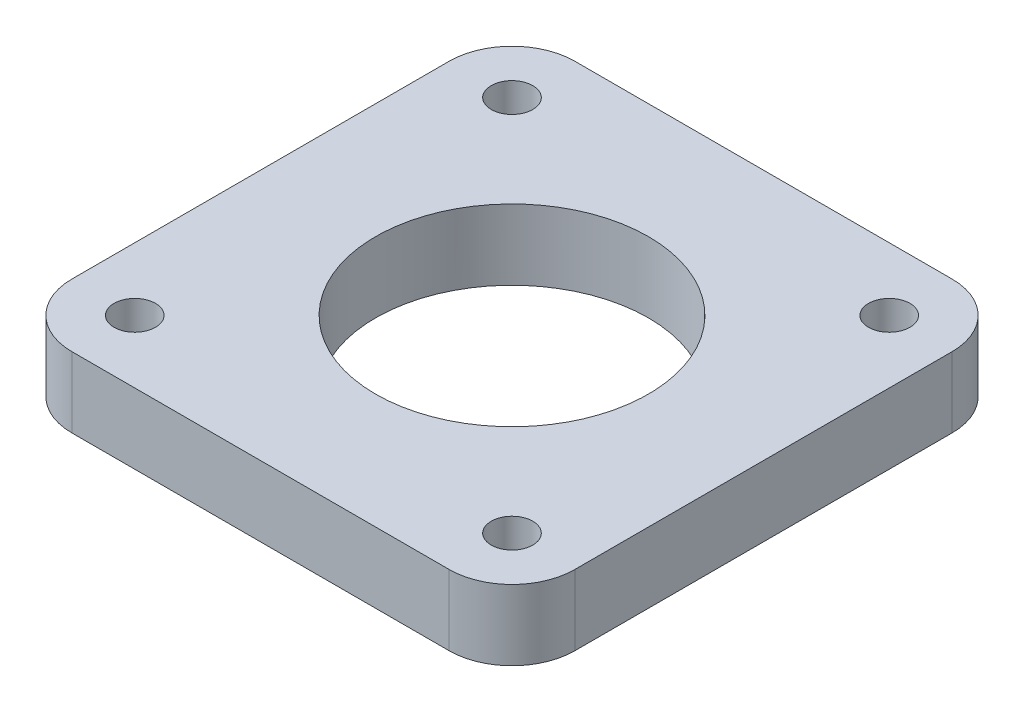
SolidWorks part; units mm, degrees
ref_plane "Front Plane" through (0, 0, 0) normal (0, 0, 1) x (1, 0, 0)
ref_plane "Top Plane" through (0, 0, 0) normal (0, 1, 0) x (1, 0, 0)
ref_plane "Right Plane" through (0, 0, 0) normal (1, 0, 0) x (0, 0, -1)
sketch "Sketch1" plane through (0, 0, 0) normal (0, 1, 0) x (1, 0, 0)
  line L0 (-20, 15) -> (-20, -15)
  line L1 (-15, 20) -> (15, 20)
  line L2 (-15, -20) -> (15, -20)
  line L3 (20, 15) -> (20, -15)
  line L4 (-20, 20) -> (20, -20) construction
  line L5 (-20, -20) -> (20, 20) construction
  arc A0 (15, -20) -> (20, -15) centre (15, -15) ccw
  arc A1 (-20, -15) -> (-15, -20) centre (-15, -15) ccw
  arc A2 (-15, 20) -> (-20, 15) centre (-15, 15) ccw
  arc A3 (15, 20) -> (20, 15) centre (15, 15) cw
  point P2 (0, 0)
  dimension "D3" = 5
  dimension "D1" = 40
  dimension "D2" = 40
extrude "Boss-Extrude1" add sketch "Sketch1" along normal blind 5.6
sketch "Sketch3" plane through (0, 0, 0) normal (0, -1, 0) x (-1, 0, 0)
  circle A0 centre (0, 0) radius 10.85
  dimension "D1" = 21.7
extrude "Cut-Extrude2" cut sketch "Sketch3" against normal blind 7.5
sketch "Sketch5" plane through (0, 5.6, 0) normal (0, 1, 0) x (1, 0, 0)
  line L0 (15, 20) -> (-15, 20) construction
  line L2 (-20, 15) -> (-20, -15) construction
  line L3 (0, 20) -> (0, -20) construction
  line L4 (-15, -20) -> (15, -20) construction
  line L5 (-20, 0) -> (20, 0) construction
  line L6 (20, -15) -> (20, 15) construction
  circle A0 centre (-15, 15) radius 1.65
  circle A1 centre (15, 15) radius 1.65
  circle A2 centre (15, -15) radius 1.65
  circle A3 centre (-15, -15) radius 1.65
  dimension "D1" = 5
  dimension "D3" = 3.3
  dimension "D2" = 5
extrude "Cut-Extrude4" cut sketch "Sketch5" against normal through all
